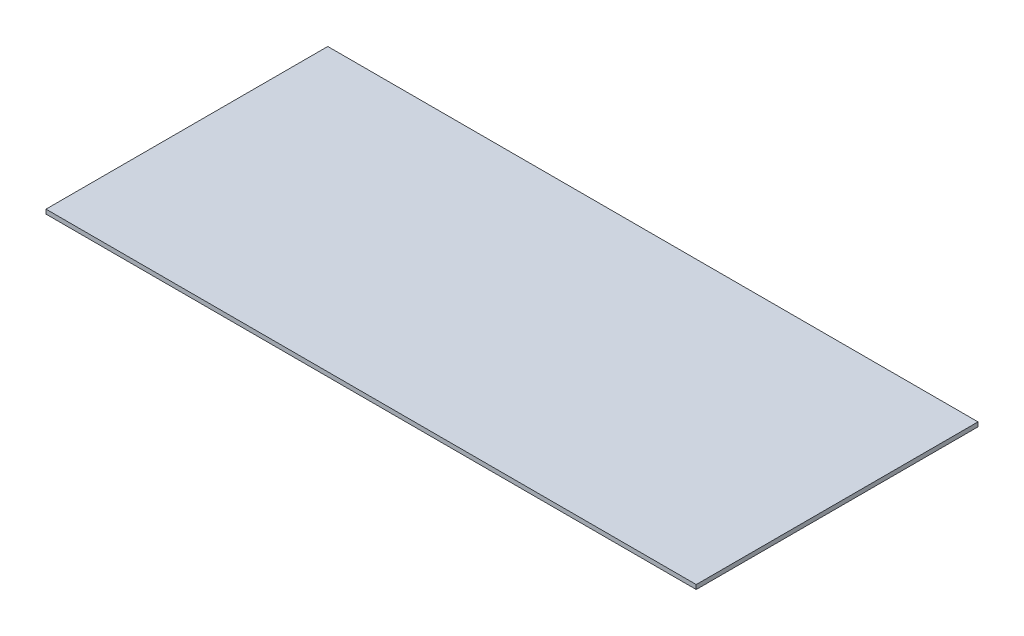
SolidWorks part; units mm, degrees
ref_plane "Front Plane" through (0, 0, 0) normal (0, 0, 1) x (1, 0, 0)
ref_plane "Top Plane" through (0, 0, 0) normal (0, 1, 0) x (1, 0, 0)
ref_plane "Right Plane" through (0, 0, 0) normal (1, 0, 0) x (0, 0, -1)
sketch "Sketch1" plane through (0, 0, 0) normal (0, 1, 0) x (1, 0, 0)
  line L1 (-190.5, -82.55) -> (190.5, -82.55)
  line L2 (-190.5, -82.55) -> (-190.5, 82.55)
  line L3 (-190.5, 82.55) -> (190.5, 82.55)
  line L4 (190.5, -82.55) -> (190.5, 82.55)
  line L5 (-190.5, -82.55) -> (190.5, 82.55) construction
  line L6 (-190.5, 82.55) -> (190.5, -82.55) construction
  point P0 (0, 0)
  dimension "D1" = 165.1
  dimension "D2" = 381
extrude "Boss-Extrude1" add sketch "Sketch1" along normal blind 2.54
